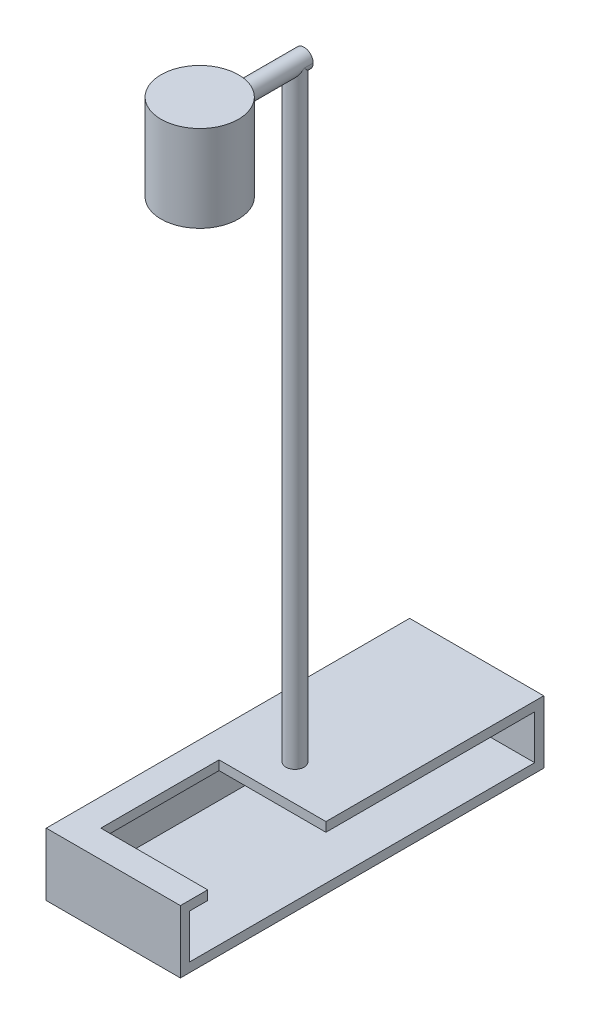
SolidWorks part; units mm, degrees
ref_plane "Front Plane" through (0, 0, 0) normal (0, 0, 1) x (1, 0, 0)
ref_plane "Top Plane" through (0, 0, 0) normal (0, 1, 0) x (1, 0, 0)
ref_plane "Right Plane" through (0, 0, 0) normal (1, 0, 0) x (0, 0, -1)
sketch "Sketch1" plane through (0, 0, 0) normal (0, 0, 1) x (1, 0, 0)
  line L1 (-14.75, -6.895) -> (14.75, -6.895)
  line L2 (-14.75, -6.895) -> (-14.75, 6.895)
  line L3 (-14.75, 6.895) -> (14.75, 6.895)
  line L4 (14.75, -6.895) -> (14.75, 6.895)
  line L5 (-14.75, -6.895) -> (14.75, 6.895) construction
  line L6 (-14.75, 6.895) -> (14.75, -6.895) construction
  point P0 (0, 0)
  dimension "D1" = 29.5
  dimension "D2" = 13.79
sketch "Sketch3" plane through (0, 0, 0) normal (0, 1, 0) x (1, 0, 0)
  circle A0 centre (0, -39.95) radius 2.5
  point P2 (0, 0)
  dimension "D2" = 5
  dimension "D1" = 39.95
sketch "Sketch4" plane through (0, 0, 0) normal (0, 1, 0) x (1, 0, 0)
  circle A0 centre (0, -39.95) radius 2
  dimension "D1" = 4
  dimension "D2" = 0
extrude "Boss-Extrude1" add sketch "Sketch4" along normal blind 140 contours A0
sketch "Sketch5" plane through (0, 0, 0) normal (0, 0, 1) x (1, 0, 0)
  line L0 (-14.75, -6.895) -> (14.75, -6.895)
  line L1 (-14.75, -6.895) -> (-14.75, 6.895)
  line L2 (-14.75, 6.895) -> (14.75, 6.895)
  line L3 (14.75, -6.895) -> (14.75, 6.895)
extrude "Boss-Extrude3" add sketch "Sketch5" along normal blind 79.9
sketch "Sketch6" plane through (14.75, 0, 0) normal (1, 0, 0) x (0, 0, -1)
  line L0 (-37.45, 0) -> (-42.45, 0) construction
  line L2 (-77.9, 4.85) -> (-2, 4.85)
  line L3 (-77.9, 4.85) -> (-77.9, -4.85)
  line L4 (-77.9, -4.85) -> (-2, -4.85)
  line L5 (-2, 4.85) -> (-2, -4.85)
  line L6 (-77.9, 4.85) -> (-2, -4.85) construction
  line L7 (-77.9, -4.85) -> (-2, 4.85) construction
  point P2 (-39.95, 0)
  dimension "D1" = 9.7
  dimension "D2" = 75.9
extrude "Cut-Extrude1" cut sketch "Sketch6" against normal blind 27.5
sketch "Sketch7" plane through (0, 6.895, 0) normal (0, 1, 0) x (1, 0, 0)
  line L0 (-14.75, -79.9) -> (-14.75, 0) construction
  line L1 (-8.75, -47.9) -> (14.75, -47.9)
  line L2 (-8.75, -47.9) -> (-8.75, -73.9)
  line L3 (-8.75, -73.9) -> (14.75, -73.9)
  line L4 (14.75, -47.9) -> (14.75, -73.9)
  line L5 (-8.75, -47.9) -> (14.75, -73.9) construction
  line L6 (-8.75, -73.9) -> (14.75, -47.9) construction
  line L7 (14.75, -79.9) -> (-14.75, -79.9) construction
  line L10 (14.75, -79.9) -> (14.75, 0) construction
  point P0 (3, -60.9)
  point P7 (-8.75, -60.9)
  dimension "D1" = 26
  dimension "D2" = 0
  dimension "D3" = 6
  dimension "D4" = 6
extrude "Cut-Extrude2" cut sketch "Sketch7" against normal blind 3 contours L2 L3 L4 L1
ref_plane "Plane3" through (0, 0, 37.95) normal (0, 0, 1) x (1, 0, 0)
sketch "Sketch8" plane through (0, 0, 37.95) normal (0, 0, 1) x (1, 0, 0)
  line L0 (2, 140) -> (-2, 140) construction
  circle A0 centre (0, 140) radius 2
  point P4 (0, 0)
extrude "Boss-Extrude4" add sketch "Sketch8" along normal blind 22.95
ref_plane "Plane4" through (0, 102, 0) normal (0, 1, 0) x (1, 0, 0)
ref_plane "Plane8" through (0, 140, 0) normal (0, 1, 0) x (1, 0, 0)
sketch "Sketch12" plane through (0, 140, 0) normal (0, 1, 0) x (1, 0, 0)
  circle A2 centre (0, -60.9) radius 8.5
  dimension "D1" = 17
extrude "Boss-Extrude6" add sketch "Sketch12" against normal blind 15.01
sketch "Sketch13" plane through (0, 140, 0) normal (0, 1, 0) x (1, 0, 0)
  circle A0 centre (0, -60.9) radius 8.5
  dimension "D1" = 17
extrude "Boss-Extrude7" add sketch "Sketch13" along normal blind 4
ref_plane "Plane7" through (14.75, -4.85, 2) normal (0, 1, 0) x (1, 0, 0)
sketch "Sketch14" plane through (0, 124.99, 0) normal (0, -1, 0) x (1, 0, 0)
  circle A0 centre (0, 60.9) radius 6.5
  dimension "D1" = 13
extrude "Cut-Extrude3" cut sketch "Sketch14" against normal blind 12
